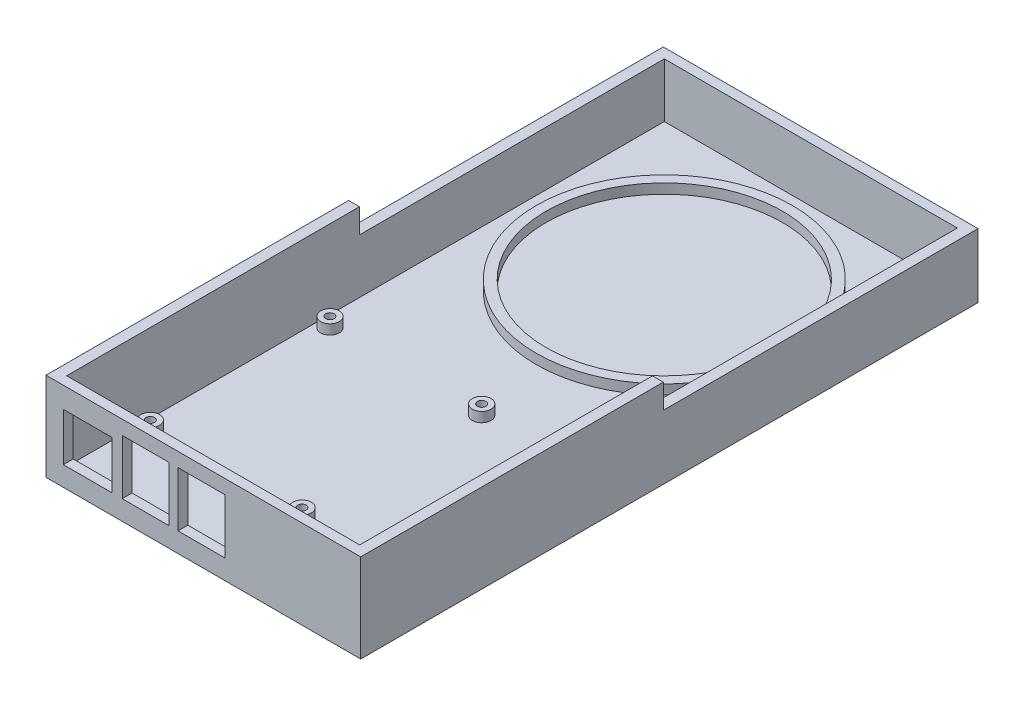
SolidWorks part; units mm, degrees
ref_plane "Front Plane" through (0, 0, 0) normal (0, 0, 1) x (1, 0, 0)
ref_plane "Top Plane" through (0, 0, 0) normal (0, 1, 0) x (1, 0, 0)
ref_plane "Right Plane" through (0, 0, 0) normal (1, 0, 0) x (0, 0, -1)
sketch "Sketch2" plane through (0, 0, 0) normal (0, 0, 1) x (1, 0, 0)
  line L0 (0, 3.175) -> (101.6, 3.175)
  line L1 (0, 0) -> (101.6, 0)
  line L2 (0, 0) -> (0, 3.175)
  line L4 (101.6, 0) -> (101.6, 3.175)
  dimension "D1" = 3.175
  dimension "D2" = 101.6
extrude "Boss-Extrude1" add sketch "Sketch2" along normal blind 199.3
sketch "Sketch3" plane through (0, 3.175, 0) normal (0, 1, 0) x (1, 0, 0)
  line L0 (0, -199.3) -> (101.6, -199.3)
  line L9 (3.5, -3.175) -> (98.1, -3.175)
  line L10 (3.5, -3.175) -> (3.5, -196.125)
  line L11 (3.5, -196.125) -> (98.1, -196.125)
  line L12 (98.1, -3.175) -> (98.1, -196.125)
  line L13 (0, 0) -> (101.6, 0)
  line L14 (0, 0) -> (0, -199.3)
  line L16 (101.6, 0) -> (101.6, -199.3)
  line L17 (50.8, 0) -> (50.8, -199.3) construction
  line L18 (101.6, -99.65) -> (0, -99.65) construction
  dimension "D1" = 3.175
  dimension "D2" = 3.5
extrude "Boss-Extrude2" add sketch "Sketch3" along normal blind 25.4
sketch "Sketch5" plane through (0, 3.175, 0) normal (0, 1, 0) x (1, 0, 0)
  line L0 (50.8, -50.475) -> (50.8, 0) construction
  line L1 (101.6, 0) -> (0, 0) construction
  line L11 (3.5, -3.175) -> (50.8, -50.475) construction
  line L12 (98.1, -3.175) -> (3.5, -3.175) construction
  circle A0 centre (50.8, -50.475) radius 38.1635
  circle A1 centre (50.8, -50.475) radius 41.3385
  dimension "D1" = 76.327
  dimension "D2" = 45
  dimension "D3" = 3.175
extrude "Boss-Extrude4" add sketch "Sketch5" along normal blind 3.175
sketch "Sketch7" plane through (0, 3.175, 0) normal (0, 1, 0) x (1, 0, 0)
  line L0 (31.627, -111.125) -> (31.627, -196.125) construction
  line L1 (3.5, -3.175) -> (3.5, -196.125) construction
  line L2 (3.5, -196.125) -> (98.1, -196.125) construction
  line L3 (3.5, -111.125) -> (98.1, -111.125) construction
  line L6 (98.1, -196.125) -> (98.1, -3.175) construction
  line L7 (3.5, -196.125) -> (98.1, -196.125) construction
  circle A4 centre (7.127, -172.752) radius 3
  circle A5 centre (7.127, -172.752) radius 1.375
  circle A14 centre (7.127, -114.752) radius 3
  circle A15 centre (7.127, -114.752) radius 1.375
  circle A16 centre (56.127, -172.752) radius 3
  circle A17 centre (56.127, -172.752) radius 1.375
  circle A18 centre (56.127, -114.752) radius 1.375
  circle A19 centre (56.127, -114.752) radius 3
  dimension "D1" = 6
  dimension "D2" = 2.75
  dimension "D3" = 58
  dimension "D7" = 24.5
  dimension "D4" = 3.627
  dimension "D5" = 3.627
  dimension "D6" = 85
extrude "Boss-Extrude5" add sketch "Sketch7" along normal blind 3.175
sketch "Sketch8" plane through (0, 0, 199.3) normal (0, 0, 1) x (1, 0, 0)
  line L0 (0, 0) -> (101.6, 0) construction
  line L1 (5.5828, 21.8186) -> (21.2673, 21.8186)
  line L2 (5.5828, 21.8186) -> (5.5828, 6.35)
  line L3 (5.5828, 6.35) -> (21.2673, 6.35)
  line L4 (21.2673, 21.8186) -> (21.2673, 6.35)
  line L5 (13.425, 21.8186) -> (13.425, 6.35) construction
  line L6 (50.175, 6.35) -> (50.175, 24.0411) construction
  line L7 (3.175, 28.575) -> (3.175, 0) construction
  line L8 (0, 28.575) -> (101.6, 28.575) construction
  line L9 (32.175, 24.0411) -> (32.175, 6.35) construction
  line L10 (24.6185, 24.0411) -> (39.7315, 24.0411)
  line L11 (24.6185, 24.0411) -> (24.6185, 6.35)
  line L12 (24.6185, 6.35) -> (39.7315, 6.35)
  line L13 (39.7315, 24.0411) -> (39.7315, 6.35)
  line L14 (42.6185, 24.0411) -> (57.7315, 24.0411)
  line L15 (42.6185, 24.0411) -> (42.6185, 6.35)
  line L16 (42.6185, 6.35) -> (57.7315, 6.35)
  line L17 (57.7315, 24.0411) -> (57.7315, 6.35)
  line L18 (59.175, 28.575) -> (59.175, 0) construction
  line L19 (50.8, 0) -> (50.8, 28.575) construction
  line L21 (0, 28.575) -> (0, 0) construction
  dimension "D1" = 15.4686
  dimension "D2" = 6.35
  dimension "D3" = 15.6845
  dimension "D4" = 10.25
  dimension "D5" = 29
  dimension "D6" = 15.113
  dimension "D7" = 47
  dimension "D8" = 17.6911
  dimension "D9" = 56
  dimension "D10" = 3.175
extrude "Cut-Extrude1" cut sketch "Sketch8" against normal blind 3.175
sketch "Sketch9" plane through (0, 3.175, 0) normal (0, 1, 0) x (1, 0, 0)
  circle A0 centre (7.127, -114.752) radius 1.375
  circle A1 centre (56.127, -114.752) radius 1.375
  circle A2 centre (56.127, -172.752) radius 1.375
  circle A3 centre (7.127, -172.752) radius 1.375
  circle A6 centre (7.127, -114.752) radius 1.375 construction
  circle A7 centre (7.127, -172.752) radius 1.375 construction
  circle A8 centre (56.127, -172.752) radius 1.375 construction
  circle A9 centre (56.127, -114.752) radius 1.375 construction
  point P12 (22.4295, -124.5774)
  point P13 (0, 0)
  dimension "D1" = 2.75
extrude "Cut-Extrude2" cut sketch "Sketch9" against normal blind 3.175
sketch "Sketch10" plane through (0, 28.575, 0) normal (0, 1, 0) x (1, 0, 0)
  line L0 (101.6, -199.3) -> (101.6, 0) construction
  line L1 (0, 0) -> (101.6, 0)
  line L2 (0, 0) -> (0, -101.6)
  line L3 (0, -101.6) -> (101.6, -101.6)
  line L4 (101.6, 0) -> (101.6, -101.6)
extrude "Cut-Extrude3" cut sketch "Sketch10" against normal blind 7.874
